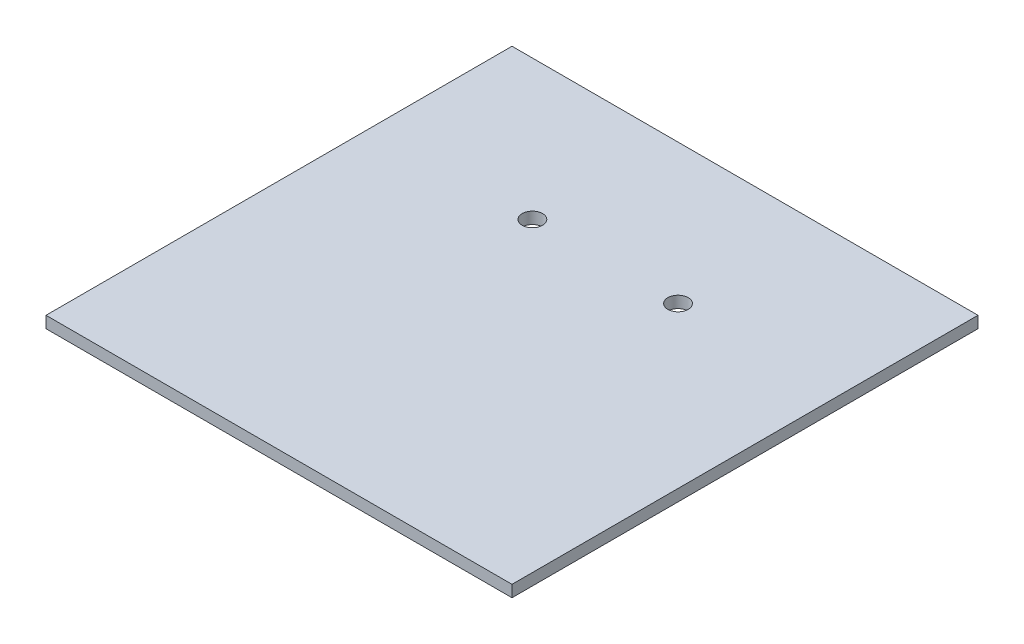
SolidWorks part; units mm, degrees
ref_plane "Plan de face" through (0, 0, 0) normal (0, 0, 1) x (1, 0, 0)
ref_plane "Plan de dessus" through (0, 0, 0) normal (0, 1, 0) x (1, 0, 0)
ref_plane "Plan de droite" through (0, 0, 0) normal (1, 0, 0) x (0, 0, -1)
sketch "Esquisse1" plane through (0, 0, 0) normal (0, 1, 0) x (1, 0, 0)
  line L1 (0, 0) -> (80, 0)
  line L2 (0, 0) -> (0, 80)
  line L3 (0, 80) -> (80, 80)
  line L4 (80, 0) -> (80, 80)
  dimension "D1" = 80
  dimension "D2" = 80
extrude "Boss.-Extru.1" add sketch "Esquisse1" along normal blind 2
sketch "Esquisse2" plane through (0, 2, 0) normal (0, 1, 0) x (1, 0, 0)
  line L0 (0, 0) -> (80, 0) construction
  line L1 (40, 0) -> (40, 36.4662) construction
  line L2 (80, 80) -> (0, 80) construction
  circle A0 centre (27.5, 56) radius 1.75
  circle A1 centre (52.5, 56) radius 1.75
  dimension "D1" = 3.5
  dimension "D2" = 24
  dimension "D3" = 12.5
extrude "Enlèv. mat.-Extru.1" cut sketch "Esquisse2" against normal up to next
